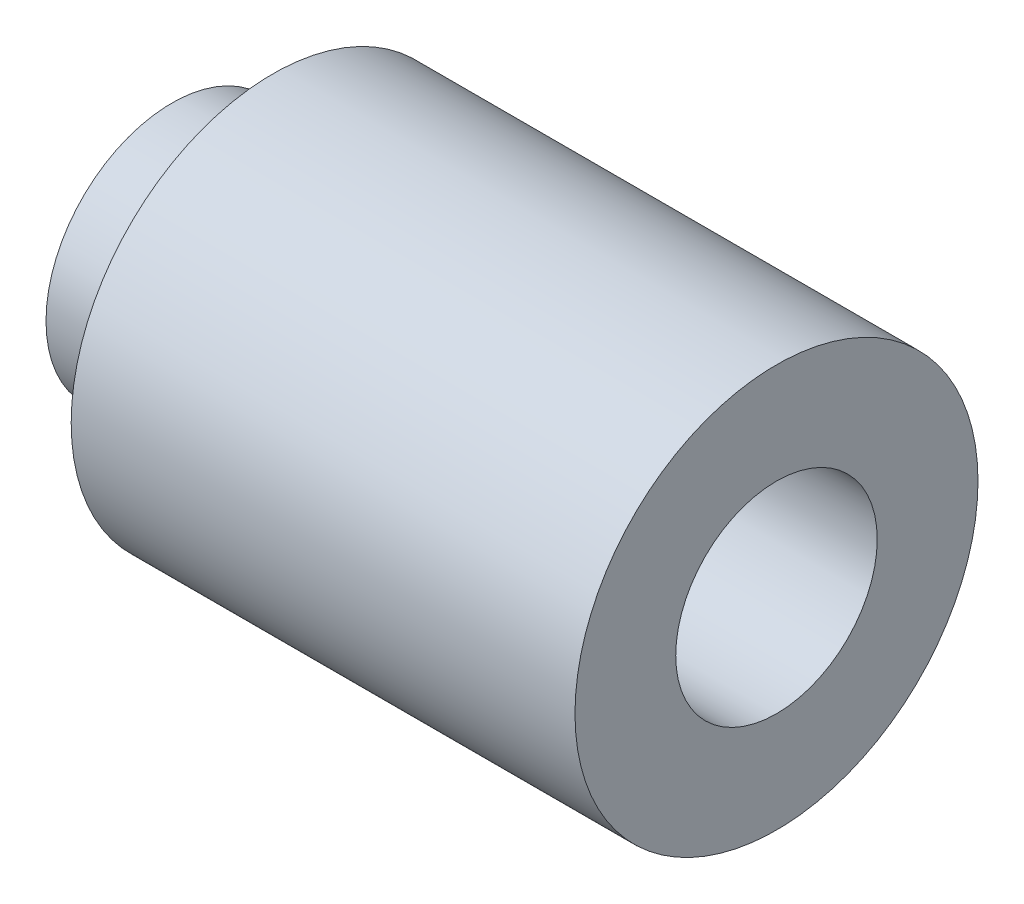
SolidWorks part; units mm, degrees
ref_plane "Front Plane" through (0, 0, 0) normal (0, 0, 1) x (1, 0, 0)
ref_plane "Top Plane" through (0, 0, 0) normal (0, 1, 0) x (1, 0, 0)
ref_plane "Right Plane" through (0, 0, 0) normal (1, 0, 0) x (0, 0, -1)
sketch "Sketch1" plane through (0, 0, 0) normal (1, 0, 0) x (0, 0, -1)
  circle A0 centre (0, 0) radius 2
  circle A1 centre (0, 0) radius 4
extrude "Boss-Extrude1" add sketch "Sketch1" along normal blind 10
sketch "Sketch2" plane through (0, 0, 0) normal (-1, 0, 0) x (0, 0, 1)
  circle A0 centre (0, 0) radius 2 construction
  circle A1 centre (0, 0) radius 2
  circle A2 centre (0, 0) radius 2.5
  dimension "D1" = 0.5
extrude "Boss-Extrude2" add sketch "Sketch2" along normal blind 2
